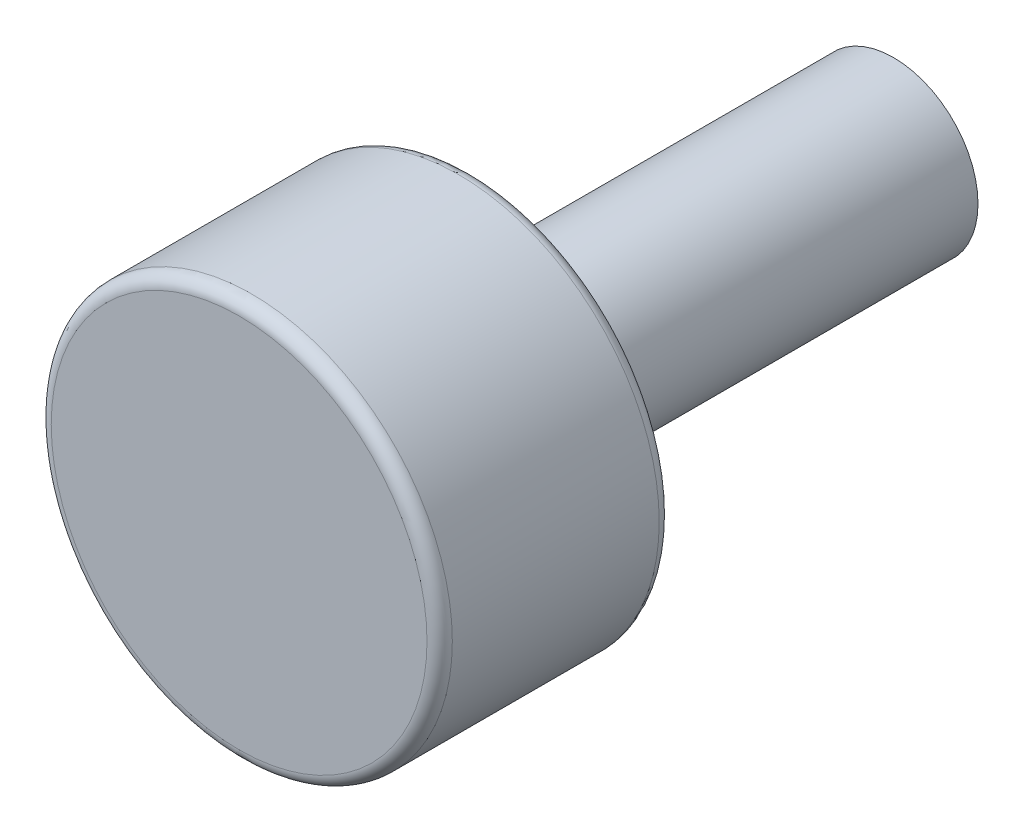
SolidWorks part; units mm, degrees
ref_plane "Front" through (0, 0, 0) normal (0, 0, 1) x (1, 0, 0)
ref_plane "Top" through (0, 0, 0) normal (0, 1, 0) x (1, 0, 0)
ref_plane "Right" through (0, 0, 0) normal (1, 0, 0) x (0, 0, -1)
sketch "Sketch1" plane through (0, 0, 0) normal (0, 0, 1) x (1, 0, 0)
  circle A0 centre (0, 0) radius 9.5
extrude "Boss-Extrude1" add sketch "Sketch1" along normal blind 11
sketch "Sketch2" plane through (0, 0, 0) normal (0, 0, -1) x (-1, 0, 0)
  circle A0 centre (0, 0) radius 4
extrude "Boss-Extrude2" add sketch "Sketch2" along normal blind 20
fillet "Fillet1" radius 0.6 1 edges at (9.5, 0, 11)
fillet "Fillet2" radius 0.6 1 edges at (9.5, 0, 0)
